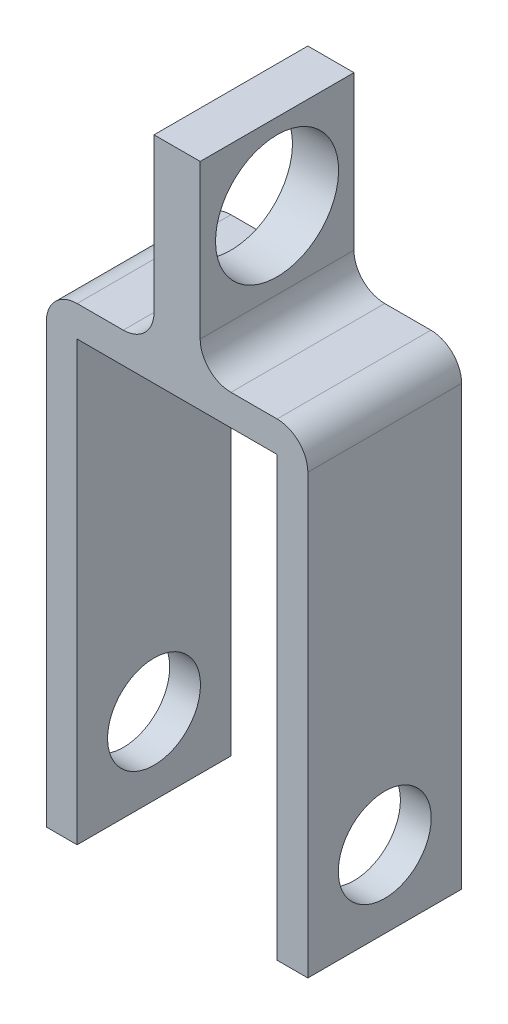
SolidWorks part; units mm, degrees
ref_plane "Front Plane" through (0, 0, 0) normal (0, 0, 1) x (1, 0, 0)
ref_plane "Top Plane" through (0, 0, 0) normal (0, 1, 0) x (1, 0, 0)
ref_plane "Right Plane" through (0, 0, 0) normal (1, 0, 0) x (0, 0, -1)
sketch "Sketch1" plane through (0, 0, 0) normal (0, 0, 1) x (1, 0, 0)
  line L1 (-7.5, 35) -> (7.5, 35)
  line L2 (-7.5, 35) -> (-7.5, -35)
  line L3 (-7.5, -35) -> (7.5, -35)
  line L4 (7.5, 35) -> (7.5, -35)
  line L5 (-7.5, 35) -> (7.5, -35) construction
  line L6 (-7.5, -35) -> (7.5, 35) construction
  line L7 (-42.5, -25) -> (42.5, -25)
  line L8 (-42.5, -25) -> (-42.5, -35)
  line L9 (-42.5, -35) -> (42.5, -35)
  line L10 (42.5, -25) -> (42.5, -35)
  line L11 (-42.5, -25) -> (-32.5, -25)
  line L12 (-42.5, -25) -> (-42.5, -177.4)
  line L13 (-42.5, -177.4) -> (-32.5, -177.4)
  line L14 (-32.5, -25) -> (-32.5, -177.4)
  line L15 (42.5, -25) -> (32.5, -25)
  line L16 (42.5, -25) -> (42.5, -177.4)
  line L17 (42.5, -177.4) -> (32.5, -177.4)
  line L18 (32.5, -25) -> (32.5, -177.4)
  point P0 (0, 0)
  point P10 (0, -35)
  dimension "D1" = 85
  dimension "D2" = 42.5
  dimension "D3" = 10
  dimension "D4" = 15
  dimension "D5" = 70
  dimension "D6" = 10
  dimension "D7" = 10
  dimension "D8" = 152.4
extrude "Boss-Extrude1" add sketch "Sketch1" along normal blind 50 contours L14 L9 L12 L13 | L14 L7 L8 L9 | L7 L14 L9 L2 | L7 L2 L3 L4 | L2 L7 L4 L1 | L18 L7 L4 L9 | L7 L18 L9 L10 | L9 L18 L17 L16
fillet "Fillet1" radius 10 4 edges at (-7.5, -25, 25) (7.5, -25, 25) (42.5, -25, 25) (-42.5, -25, 25)
sketch "Sketch2" plane through (7.5, 0, 0) normal (1, 0, 0) x (0, 0, -1)
  line L0 (-50, 35) -> (0, 35) construction
  line L1 (-50, 35) -> (-50, -15) construction
  circle A0 centre (-25, 10) radius 20
  dimension "D1" = 40
  dimension "D2" = 25
  dimension "D3" = 25
extrude "Cut-Extrude1" cut sketch "Sketch2" against normal through all both and the other way through all
sketch "Sketch3" plane through (42.5, 0, 0) normal (1, 0, 0) x (0, 0, -1)
  line L0 (-50, -35) -> (-50, -177.4) construction
  line L1 (-50, -177.4) -> (0, -177.4) construction
  circle A0 centre (-25, -152.4) radius 15.1
  dimension "D3" = 30.2
  dimension "D1" = 25
  dimension "D2" = 25
extrude "Cut-Extrude2" cut sketch "Sketch3" against normal through all both and the other way through all
equation "\"D2@Sketch1\"=\"D1@Sketch1\"/2"
